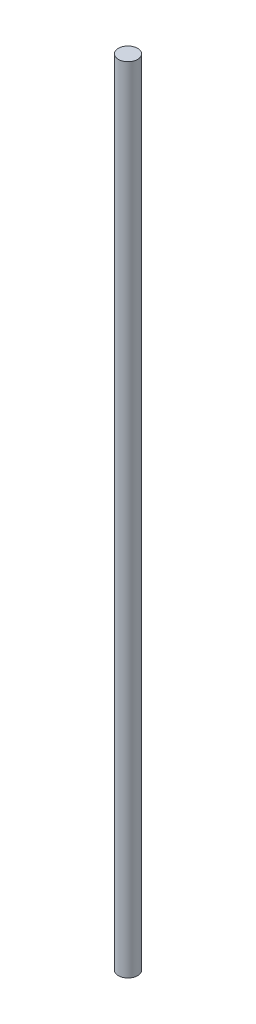
SolidWorks part; units mm, degrees
ref_plane "Front Plane" through (0, 0, 0) normal (0, 0, 1) x (1, 0, 0)
ref_plane "Top Plane" through (0, 0, 0) normal (0, 1, 0) x (1, 0, 0)
ref_plane "Right Plane" through (0, 0, 0) normal (1, 0, 0) x (0, 0, -1)
sketch "Sketch1" plane through (0, 0, 0) normal (0, 1, 0) x (1, 0, 0)
  circle A0 centre (0, 0) radius 4
  dimension "D1" = 8
extrude "Boss-Extrude1" add sketch "Sketch1" along normal blind 330
